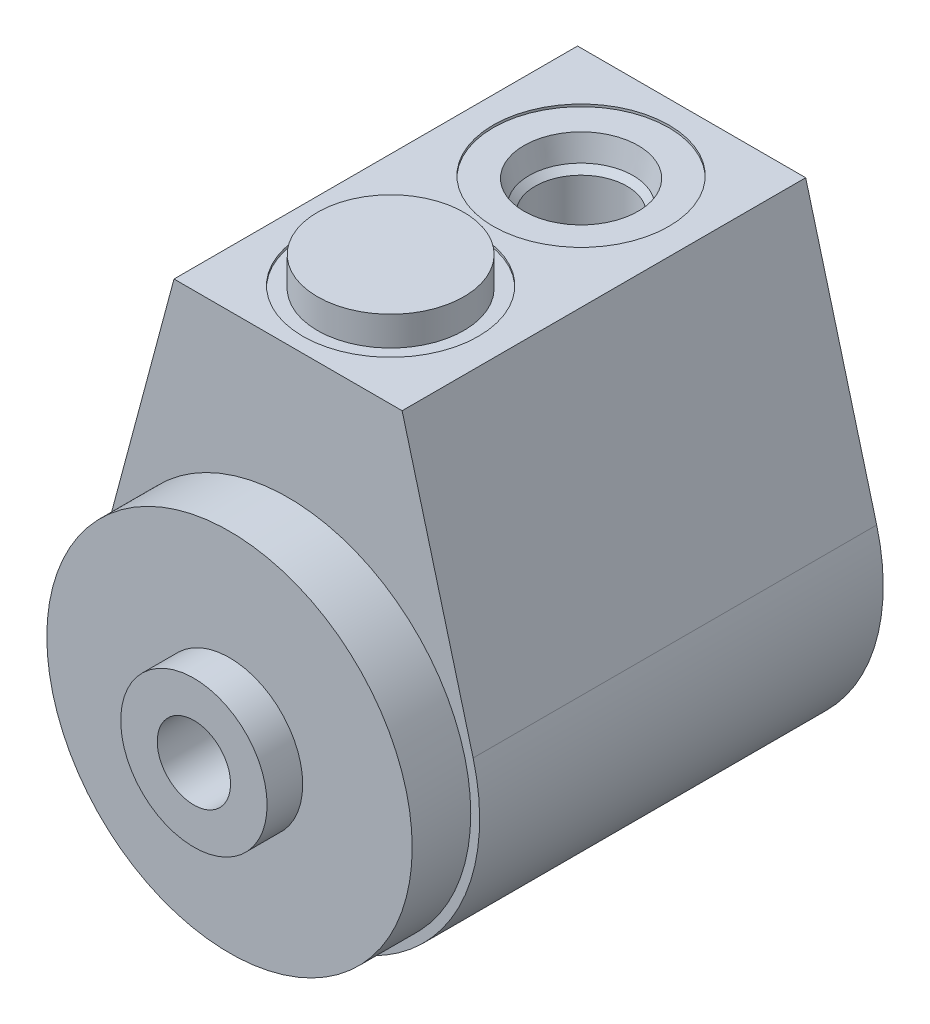
SolidWorks part; units mm, degrees
material "Alloy Steel"
ref_plane "Front Plane" through (0, 0, 0) normal (0, 0, 1) x (1, 0, 0)
ref_plane "Top Plane" through (0, 0, 0) normal (0, 1, 0) x (1, 0, 0)
ref_plane "Right Plane" through (0, 0, 0) normal (1, 0, 0) x (0, 0, -1)
ref_plane "Plane1" through (0, 0, 43.7642) normal (0, 0, 1) x (1, 0, 0)
sketch "Sketch1" plane through (0, 0, 43.7642) normal (0, 0, 1) x (1, 0, 0)
  line L0 (20.0704, 5.3731) -> (12.3698, 34.1376)
  line L1 (12.3698, 34.1376) -> (-12.3698, 34.1376)
  line L2 (-12.3698, 34.1376) -> (-20.0704, 5.3731)
  line L3 (0, 0) -> (0, 50.6803) construction
  arc A0 (-20.0704, 5.3731) -> (20.0704, 5.3731) centre (0, 0) ccw
  dimension "D1" = 41.5544
  dimension "D2" = 34.1376
  dimension "D3" = 12.3698
extrude "Extrude1" add sketch "Sketch1" against normal blind 43.7642
hole_wizard "Hole1" positions "Sketch3" profile "Sketch2" legacy
sketch "Sketch3" plane through (0, 34.1376, 0) normal (0, 1, 0) x (-1, 0, 0)
  line L0 (-12.3698, 43.7642) -> (12.3698, 43.7642) construction
  point P0 (0, 32.639)
  dimension "D1" = 11.1252
sketch "Sketch2" plane through (0, 34.1376, 32.639) normal (1, 0, 0) x (0, 0, 1)
  line L0 (0, 0) -> (0, 0.254)
  line L1 (0, 0.254) -> (9.525, 0.254)
  line L2 (9.525, 0.254) -> (9.525, 0)
  line L3 (9.525, 0) -> (0, 0)
  line L4 (0, 110) -> (0, -10) construction
  dimension "Diameter" = 19.05
  dimension "Depth" = 0.254
hole_wizard "Hole2" positions "Sketch5" profile "Sketch4" legacy
sketch "Sketch5" plane through (0, 0, 0) normal (0, 0, -1) x (-1, 0, 0)
  point P0 (0, 0)
sketch "Sketch4" plane through (0, 0, 0) normal (1, 0, 0) x (0, 1, 0)
  line L0 (0, 0) -> (0, 4.826)
  line L1 (0, 4.826) -> (10.287, 4.826)
  line L2 (10.287, 4.826) -> (10.287, 0)
  line L3 (10.287, 0) -> (0, 0)
  line L4 (0, 110) -> (0, -10) construction
  dimension "Diameter" = 20.574
  dimension "Depth" = 4.826
ref_plane "Plane2" through (0, 0, 0) normal (0, -1, 0) x (1, 0, 0)
sketch "Sketch7" plane through (0, 0, 0) normal (0, -1, 0) x (1, 0, 0)
  line L0 (7.9375, 53.975) -> (0, 53.975)
  line L1 (0, 53.975) -> (0, 43.7642)
  line L2 (0, 43.7642) -> (19.812, 43.7642)
  line L3 (19.812, 43.7642) -> (19.812, 50.1142)
  line L4 (19.812, 50.1142) -> (7.9375, 50.1142)
  line L5 (7.9375, 50.1142) -> (7.9375, 53.975)
  line L6 (0, 0) -> (0, 59.8975) construction
  line L7 (20.7772, 43.7642) -> (-20.7772, 43.7642) construction
  line L8 (-20.7772, 0) -> (20.7772, 0) construction
  dimension "D1" = 15.875
  dimension "D2" = 39.624
  dimension "D3" = 6.35
  dimension "D4" = 53.975
revolve "Revolve2" add sketch "Sketch7" angle 360 about L6
sketch "Sketch6" plane through (0, 0, 0) normal (0, -1, 0) x (1, 0, 0)
  line L0 (7.9375, 4.826) -> (0, 4.826)
  line L1 (0, 4.826) -> (0, 3.8354)
  line L2 (0, 3.8354) -> (7.9375, 3.8354)
  line L3 (7.9375, 3.8354) -> (7.9375, 4.826)
  line L4 (-10.287, 4.826) -> (10.287, 4.826) construction
  line L5 (7.9375, 53.975) -> (-7.9375, 53.975) construction
  line L6 (0, 0) -> (0, 20.5953) construction
  dimension "D1" = 50.1396
  dimension "D2" = 15.875
revolve "Revolve1" add sketch "Sketch6" angle 360 about L6
ref_plane "Plane3" through (0, 0, 32.639) normal (0, 0, -1) x (-1, 0, 0)
sketch "Sketch8" plane through (0, 0, 32.639) normal (0, 0, -1) x (-1, 0, 0)
  line L0 (-7.9375, 33.8836) -> (0, 33.8836)
  line L1 (0, 33.8836) -> (0, 37.0586)
  line L2 (0, 37.0586) -> (-7.9375, 37.0586)
  line L3 (-7.9375, 37.0586) -> (-7.9375, 33.8836)
  line L4 (0, 0) -> (0, 43.9417) construction
  line L5 (9.525, 33.8836) -> (-9.525, 33.8836) construction
  dimension "D1" = 3.175
  dimension "D2" = 15.875
revolve "Revolve3" add sketch "Sketch8" angle 360 about L4
ref_plane "Plane4" through (0, 0, 11.9888) normal (0, 0, -1) x (-1, 0, 0)
sketch "Sketch9" plane through (0, 0, 11.9888) normal (0, 0, -1) x (-1, 0, 0)
  line L0 (-4.9784, 13.3096) -> (0, 13.3096)
  line L1 (0, 13.3096) -> (0, 34.1376)
  line L2 (0, 34.1376) -> (-9.525, 34.1376)
  line L3 (-9.525, 34.1376) -> (-9.525, 33.8836)
  line L4 (-9.525, 33.8836) -> (-6.1849, 33.8836)
  line L5 (-6.1849, 33.8836) -> (-5.6423, 31.3309)
  line L6 (-5.6423, 31.3309) -> (-4.9784, 30.667)
  line L7 (-4.9784, 30.667) -> (-4.9784, 13.3096)
  line L8 (0, 13.3096) -> (0, 34.1376) construction
revolve "Cut-Revolve1" cut sketch "Sketch9" angle 360 about L8
ref_plane "Plane5" through (0, 0, 32.639) normal (0, 0, 1) x (1, 0, 0)
sketch "Sketch10" plane through (0, 0, 32.639) normal (0, 0, 1) x (1, 0, 0)
  line L0 (6.1849, 33.8836) -> (0, 33.8836)
  line L1 (0, 33.8836) -> (0, 20.4216)
  line L2 (0, 20.4216) -> (4.9784, 20.4216)
  line L3 (4.9784, 20.4216) -> (4.9784, 30.667)
  line L4 (4.9784, 30.667) -> (5.6423, 31.3309)
  line L5 (5.6423, 31.3309) -> (6.1849, 33.8836)
  line L6 (0, 33.8836) -> (0, 20.4216) construction
revolve "Cut-Revolve2" cut sketch "Sketch10" angle 360 about L6
hole_wizard "Hole3" positions "Sketch12" profile "Sketch11" legacy
sketch "Sketch12" plane through (0, 0, 0) normal (0, 0, -1) x (-1, 0, 0)
  line L0 (0, 0) -> (0, -24.5872) construction
  point P0 (-15.875, 0)
  dimension "D1" = 15.875
sketch "Sketch11" plane through (15.875, 0, 0) normal (1, 0, 0) x (0, 1, 0)
  line L0 (0, 0) -> (0, 10.922)
  line L1 (0, 10.922) -> (2.5908, 10.922)
  line L2 (2.5908, 10.922) -> (2.5908, 0)
  line L3 (2.5908, 0) -> (0, 0)
  line L4 (0, 110) -> (0, -10) construction
  dimension "Diameter" = 5.1816
  dimension "Depth" = 10.922
pattern_circular "CirPattern1" count 2 over 360 about axis through (0, 0, 0) along (0, 0, 1) of "Hole3"
hole_wizard "Hole5" positions "Sketch16" profile "Sketch15" legacy
sketch "Sketch16" plane through (0, 0, 3.8354) normal (0, 0, -1) x (-1, 0, 0)
  point P0 (0, 0)
sketch "Sketch15" plane through (0, 0, 3.8354) normal (1, 0, 0) x (0, 1, 0)
  line L0 (0, 0) -> (0, 50.1396)
  line L1 (0, 50.1396) -> (3.9751, 50.1396)
  line L2 (3.9751, 50.1396) -> (3.9751, 35.7617)
  line L3 (3.9751, 35.7617) -> (5.1562, 35.052)
  line L4 (5.1562, 35.052) -> (5.1562, 0)
  line L5 (5.1562, 0) -> (0, 0)
  line L6 (0, -6.13) -> (0, 109.2824) construction
  line L7 (-3.9751, 35.7617) -> (-5.1562, 35.052) construction
  line L8 (0, 50.1396) -> (-3.9751, 50.1396) construction
  dimension "Diameter" = 7.9502
  dimension "Depth" = 50.1396
  dimension "C-Drill Diameter" = 10.3124
  dimension "C-Drill Depth" = 35.052
  dimension "C-Drill Angle" = 118
